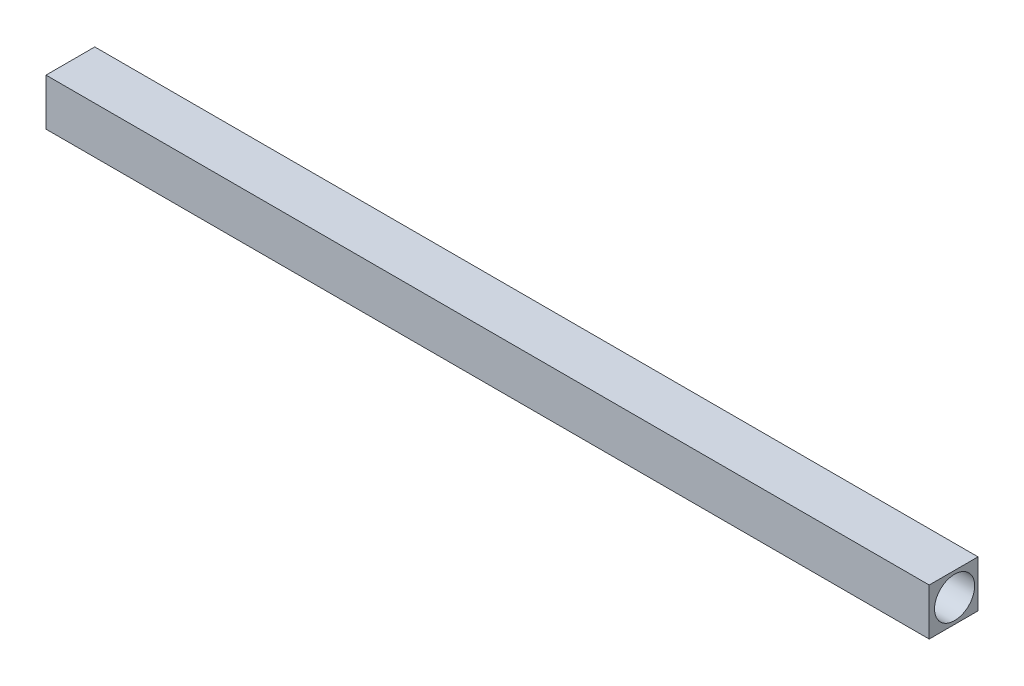
SolidWorks part; units mm, degrees
material "Malleable Cast Iron"
ref_plane "Front Plane" through (0, 0, 0) normal (0, 0, 1) x (1, 0, 0)
ref_plane "Top Plane" through (0, 0, 0) normal (0, 1, 0) x (1, 0, 0)
ref_plane "Right Plane" through (0, 0, 0) normal (1, 0, 0) x (0, 0, -1)
sketch "Sketch1" plane through (0, 0, 0) normal (0, 1, 0) x (1, 0, 0)
  line L1 (-59.3425, 0) -> (600.6575, 0)
  line L2 (-59.3425, 0) -> (-59.3425, -36.4583)
  line L3 (-59.3425, -36.4583) -> (600.6575, -36.4583)
  line L4 (600.6575, 0) -> (600.6575, -36.4583)
  dimension "D1" = 660
extrude "Boss-Extrude1" add sketch "Sketch1" along normal blind 35
sketch "Sketch2" plane through (600.6575, 0, 0) normal (1, 0, 0) x (0, 0, -1)
  circle A0 centre (-17.5, 17.5) radius 15
  dimension "D1" = 30
extrude "Cut-Extrude1" cut sketch "Sketch2" against normal through all
